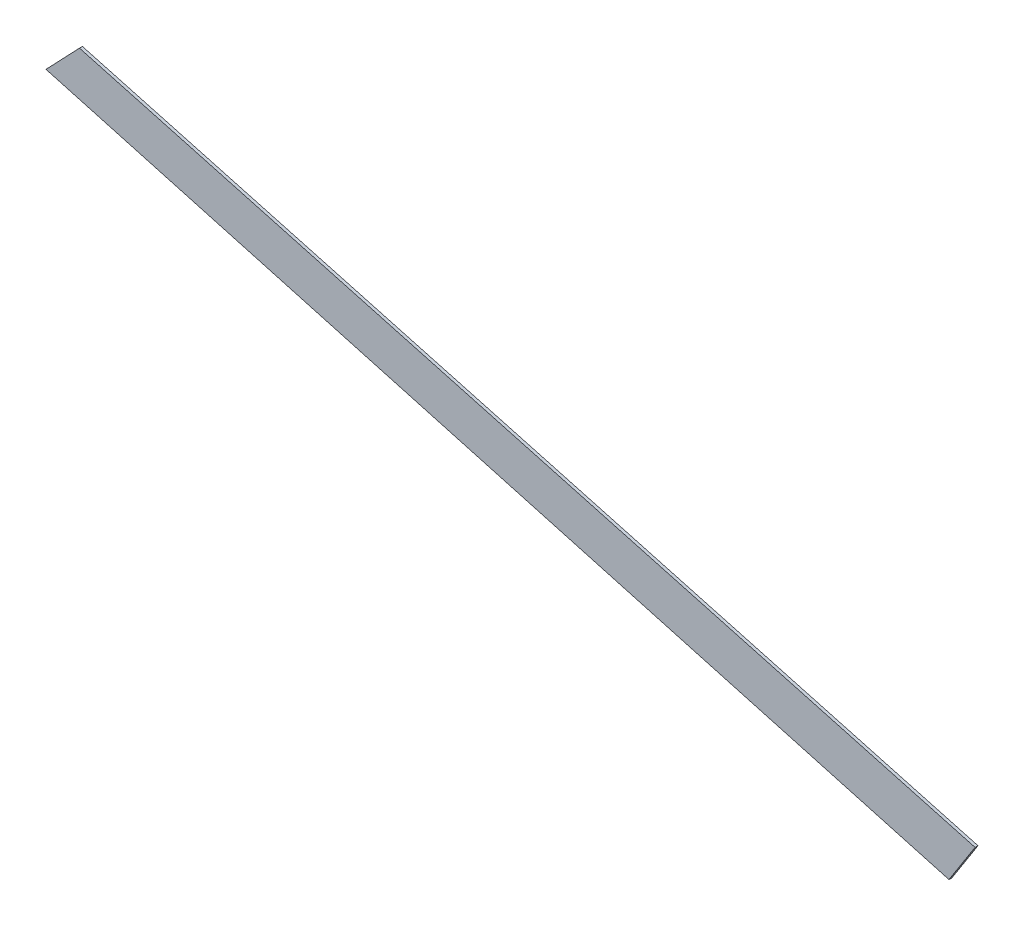
SolidWorks part; units mm, degrees
ref_plane "Front Plane" through (0, 0, 0) normal (0, 0, 1) x (1, 0, 0)
ref_plane "Top Plane" through (0, 0, 0) normal (0, 1, 0) x (1, 0, 0)
ref_plane "Right Plane" through (0, 0, 0) normal (1, 0, 0) x (0, 0, -1)
sketch3d "3DSketch1"
  line L0 (0, 0, 0) -> (-922.4717, 251.7252, 0)
  line L1 (-922.4717, 251.7252, 0) -> (-956.9694, 215.5325, 0)
  line L2 (-956.9694, 215.5325, 0) -> (-26.8947, -42.1506, 0)
  line L3 (-26.8947, -42.1506, 0) -> (0, 0, 0)
  dimension "D1" = 50
  dimension "D2" = 50
extrude "Boss-Extrude1" add sketch "3DSketch1" along direction (0, 0, 1) on the side of the normal blind 3 contours L0 L1 L2 L3
